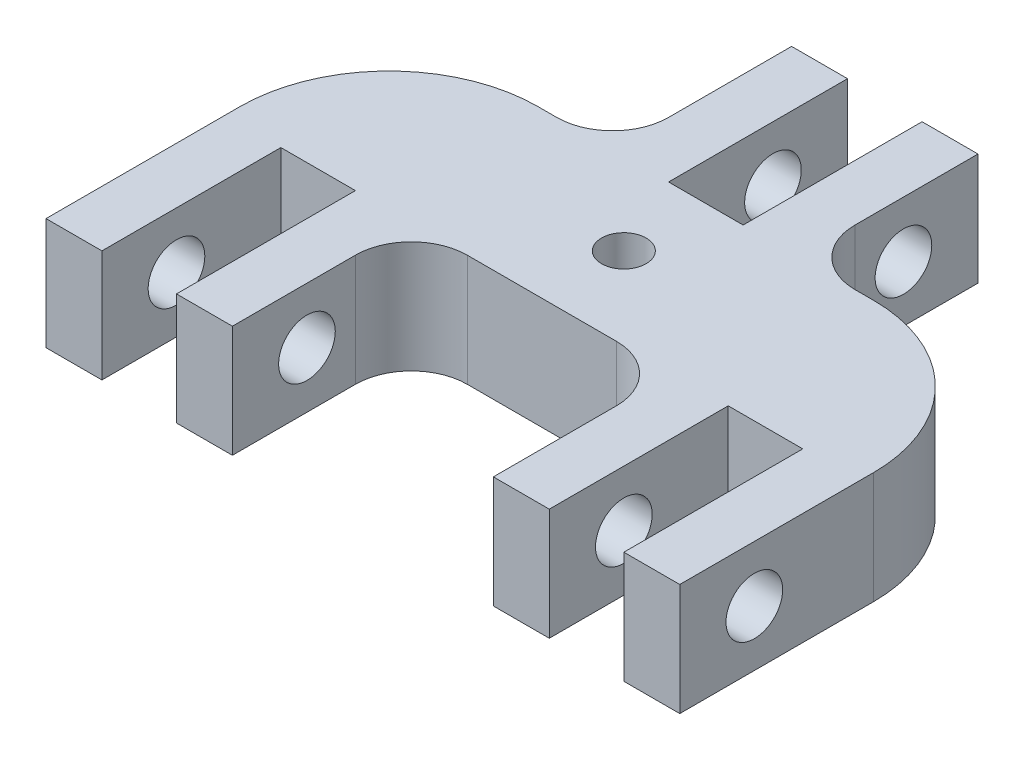
SolidWorks part; units mm, degrees
material "6061-T6 (SS)"
ref_plane "Front Plane" through (0, 0, 0) normal (0, 0, 1) x (1, 0, 0)
ref_plane "Top Plane" through (0, 0, 0) normal (0, 1, 0) x (1, 0, 0)
ref_plane "Right Plane" through (0, 0, 0) normal (1, 0, 0) x (0, 0, -1)
sketch "Sketch1" plane through (0, 0, 0) normal (0, 1, 0) x (1, 0, 0)
  line L0 (-3.175, 22.225) -> (-3.175, 6.985)
  line L1 (26.9875, -22.225) -> (22.225, -22.225)
  line L2 (26.9875, -22.225) -> (26.9875, 22.225)
  line L3 (26.9875, 22.225) -> (3.175, 22.225)
  line L4 (-26.9875, -22.225) -> (-26.9875, 22.225)
  line L5 (0, 22.225) -> (0, -22.225) construction
  line L6 (-26.9875, 0) -> (26.9875, 0) construction
  line L7 (-3.175, 6.985) -> (3.175, 6.985)
  line L8 (3.175, 6.985) -> (3.175, 22.225)
  line L9 (-15.875, -22.225) -> (-15.875, -6.985)
  line L10 (-15.875, -6.985) -> (-22.225, -6.985)
  line L11 (-22.225, -6.985) -> (-22.225, -22.225)
  line L12 (15.875, -22.225) -> (15.875, -6.985)
  line L13 (15.875, -6.985) -> (22.225, -6.985)
  line L14 (22.225, -6.985) -> (22.225, -22.225)
  line L15 (-3.175, 22.225) -> (-26.9875, 22.225)
  line L16 (-3.175, 22.225) -> (3.175, 22.225) construction
  line L17 (15.875, -22.225) -> (-15.875, -22.225)
  line L18 (-22.225, -22.225) -> (-26.9875, -22.225)
  line L19 (-19.05, -6.985) -> (-19.05, -22.225) construction
  line L20 (-17.4625, -6.985) -> (-17.4625, -22.225) construction
  line L21 (-20.6375, -6.985) -> (-20.6375, -22.225) construction
  line L22 (-20.6375, -22.225) -> (-17.4625, -22.225) construction
  point P0 (0, 0)
  dimension "D1" = 6.35
  dimension "D2" = 34.925
  dimension "D3" = 4.7625
  dimension "D4" = 15.24
  dimension "D5" = 44.45
  dimension "D6" = 3.175
extrude "Boss-Extrude1" add sketch "Sketch1" along normal blind 9.525
sketch "Sketch2" plane through (0, 9.525, 0) normal (0, 1, 0) x (1, 0, 0)
  line L0 (-7.9375, 22.225) -> (-7.9375, 6.985)
  line L1 (-3.175, 22.225) -> (-26.9875, 22.225) construction
  line L2 (-7.9375, 6.985) -> (-26.9875, 6.985)
  line L3 (-26.9875, 22.225) -> (-26.9875, -22.225) construction
  line L4 (0, 0) -> (0, -22.225) construction
  line L5 (-15.875, -22.225) -> (15.875, -22.225) construction
  line L6 (0, 0) -> (16.73, 0) construction
  line L7 (7.9375, 6.985) -> (26.9875, 6.985)
  line L8 (7.9375, 22.225) -> (7.9375, 6.985)
  line L9 (-7.9375, 6.985) -> (-26.9875, 6.985)
  line L10 (-3.175, 6.985) -> (-3.175, 22.225) construction
  line L12 (3.175, 6.985) -> (-3.175, 6.985) construction
  line L13 (-11.1125, -22.225) -> (11.1125, -22.225)
  line L14 (-11.1125, -22.225) -> (-11.1125, -6.985)
  line L15 (-11.1125, -6.985) -> (11.1125, -6.985)
  line L16 (11.1125, -22.225) -> (11.1125, -6.985)
  line L17 (15.875, -6.985) -> (22.225, -6.985) construction
  line L18 (15.875, -22.225) -> (15.875, -6.985) construction
  line L19 (-26.9875, 6.985) -> (-26.9875, 22.225)
  line L20 (-26.9875, 22.225) -> (-7.9375, 22.225)
  line L21 (7.9375, 22.225) -> (26.9875, 22.225)
  line L22 (26.9875, 22.225) -> (26.9875, 6.985)
  line M7 (-3.175, 22.225) -> (-26.9875, 22.225)
  line M8 (-26.9875, 22.225) -> (-26.9875, -22.225)
  line M13 (-15.875, -22.225) -> (15.875, -22.225)
  line M18 (26.9875, -22.225) -> (26.9875, 22.225)
  line M19 (26.9875, 22.225) -> (3.175, 22.225)
  dimension "D1" = 4.7625
  dimension "D2" = 4.7625
extrude "Cut-Extrude1" cut sketch "Sketch2" against normal through all contours L2 L0 M7 M8 | L8 L7 M19 M18 | L16 L15 L14 M13
hole_wizard "3/16 (0.1875) Clearance Dowel Hole1" positions "Sketch5" profile "Sketch4" hole size "3/16" standard "ANSI Inch" end condition through all
sketch "Sketch5" plane through (26.9875, 0, 0) normal (1, 0, 0) x (0, 0, -1)
  line L0 (-22.225, 4.7625) -> (22.225, 4.7625) construction
  line L1 (-22.225, 9.525) -> (-22.225, 0) construction
  line L2 (22.225, 0) -> (22.225, 9.525) construction
  line L5 (-6.985, 9.525) -> (-6.985, 0) construction
  line L6 (-6.985, 9.525) -> (-6.985, 0) construction
  line L11 (0, 0) -> (0, 7.7418) construction
  point P0 (-15.875, 4.7625)
  point P40 (15.875, 4.7625)
  dimension "D1" = 6.35
sketch "Sketch4" plane through (26.9875, 4.7625, 15.875) normal (0, 1, 0) x (0, 0, -1)
  line L0 (0, 0) -> (0, 53.975)
  line L1 (0, 53.975) -> (2.413, 53.975)
  line L2 (2.413, 53.975) -> (2.413, 0)
  line L5 (2.413, 0) -> (0, 0)
  line L11 (0, -6.35) -> (0, 107.95) construction
  dimension "Thru Hole Dia." = 4.826
  dimension "Thru Hole Depth" = 53.975
hole_wizard "#10-24 Tapped Hole1" positions "Sketch7" profile "Sketch6" tap size "#10-24" standard "ANSI Inch" end condition up to next
sketch "Sketch7" plane through (0, 9.525, 0) normal (0, 1, 0) x (1, 0, 0)
  point P0 (0, 0)
sketch "Sketch6" plane through (0, 9.525, 0) normal (1, 0, 0) x (0, 0, 1)
  line L0 (0, 0) -> (0, 9.525)
  line L1 (0, 9.525) -> (1.8986, 9.525)
  line L2 (1.8986, 9.525) -> (1.8986, 0)
  line L5 (1.8986, 0) -> (0, 0)
  line L11 (0, -6.35) -> (0, 107.95) construction
  dimension "Thread Major Dia." = 3.7973
  dimension "Thru Tap Drill Depth" = 9.525
fillet "Fillet1" radius 4.7625 4 edges at (-7.9375, 4.7625, -6.985) (7.9375, 4.7625, -6.985) (11.1125, 4.7625, 6.985) (-11.1125, 4.7625, 6.985)
fillet "Fillet2" radius 12.7 2 edges at (26.9875, 4.7625, -6.985) (-26.9875, 4.7625, -6.985)
